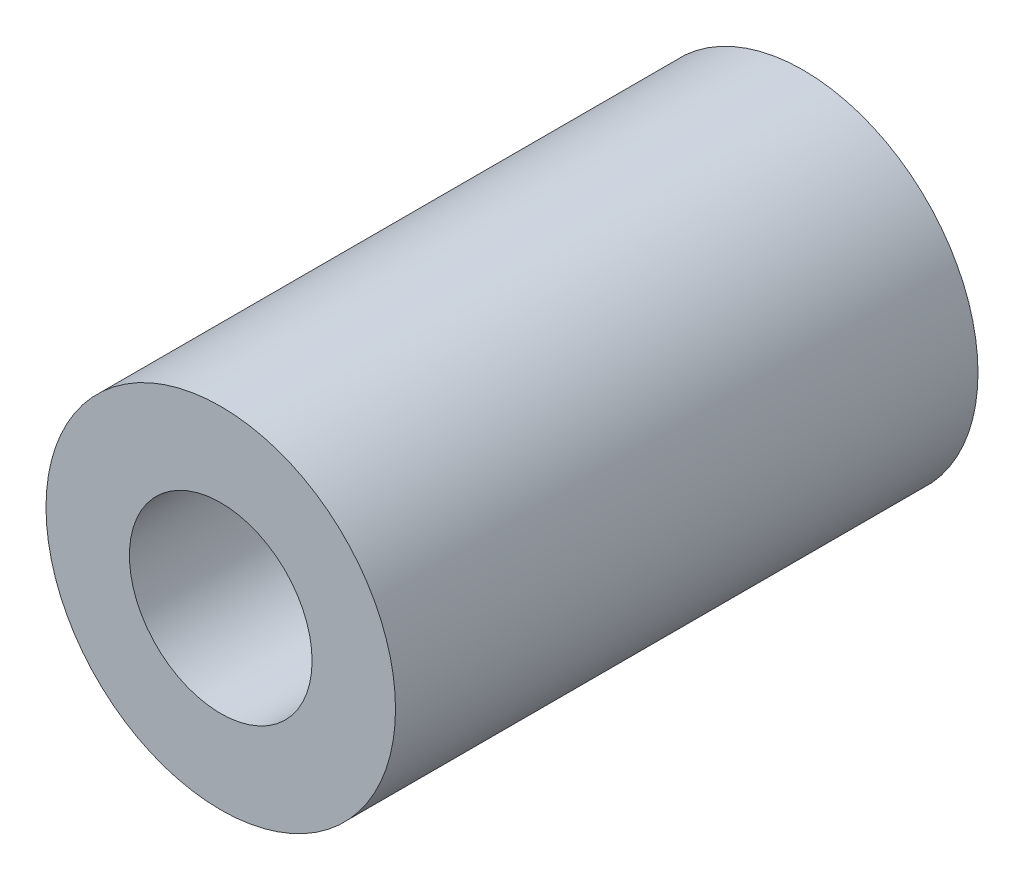
SolidWorks part; units mm, degrees
material "6061-T6 (SS)"
ref_plane "Front Plane" through (0, 0, 0) normal (0, 0, 1) x (1, 0, 0)
ref_plane "Top Plane" through (0, 0, 0) normal (0, 1, 0) x (1, 0, 0)
ref_plane "Right Plane" through (0, 0, 0) normal (1, 0, 0) x (0, 0, -1)
sketch "Sketch1" plane through (0, 0, 0) normal (0, 0, 1) x (1, 0, 0)
  circle A0 centre (0, 0) radius 4.7625
  circle A1 centre (0, 0) radius 2.4892
  dimension "D1" = 4.9784
  dimension "D2" = 9.525
extrude "Boss-Extrude1" add sketch "Sketch1" along normal mid plane 15.875 contours A0 A1
